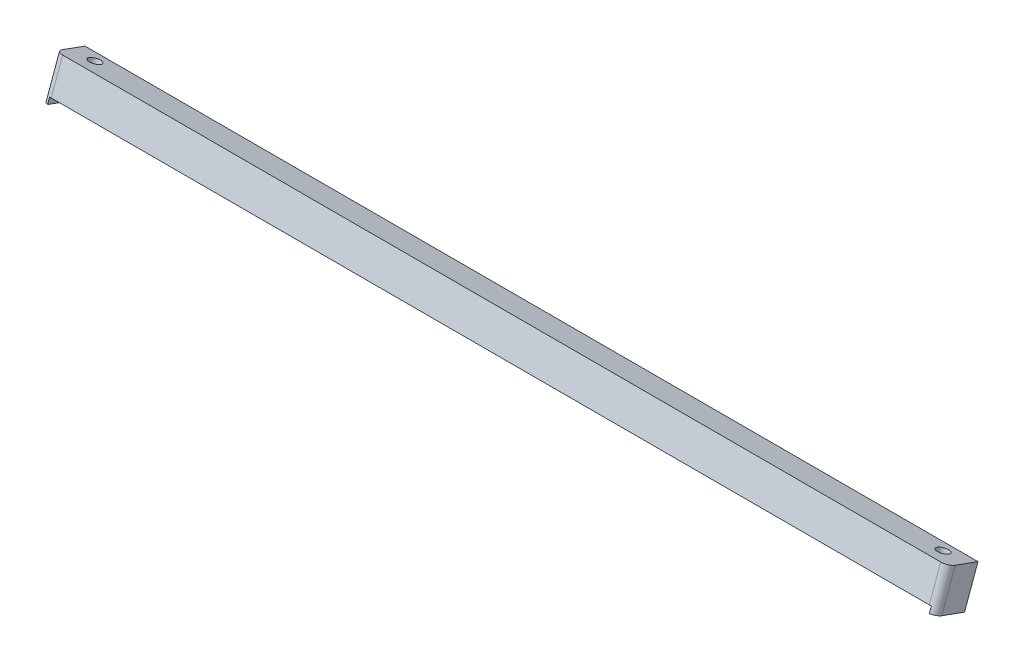
SolidWorks part; units mm, degrees
material "ABS"
ref_plane "Front Plane" through (0, 0, 0) normal (0, 0, 1) x (1, 0, 0)
ref_plane "Top Plane" through (0, 0, 0) normal (0, 1, 0) x (1, 0, 0)
ref_plane "Right Plane" through (0, 0, 0) normal (1, 0, 0) x (0, 0, -1)
sketch "Sketch1" plane through (0, 0, 0) normal (1, 0, 0) x (0, 0, -1)
  line L0 (2.5431, 8.3785) -> (-0.1316, 1.0298)
  line L1 (-0.1316, 1.0298) -> (-8.119, 3.937)
  line L3 (3.1176, 9.9569) -> (-4.8698, 12.8641)
  line L5 (-8.119, 3.937) -> (-4.8698, 12.8641)
  line L6 (2.5431, 8.3785) -> (3.1176, 9.9569)
  dimension "D1" = 8.5
  dimension "D2" = 9.5
extrude "Boss-Extrude1" add sketch "Sketch1" along normal blind 239
sketch "Sketch2" plane through (0, 9.7942, -3.5648) normal (0, 0.9397, -0.342) x (1, 0, 0)
  line L0 (119.5, 1.8524) -> (119.5, -8.9759) construction
  line L1 (240, -10.3299) -> (230.3386, -10.3299) construction
  line L2 (240, -10.3299) -> (240, -0.5476) construction
  line L3 (240, -0.5476) -> (230.3386, -0.5476) construction
  line L4 (230.3386, -10.3299) -> (230.3386, -0.5476) construction
  line L6 (239, -8.9759) -> (0, -8.9759) construction
  line L7 (8.6614, -10.3299) -> (8.6614, -0.5476) construction
  line L8 (-1, -0.5476) -> (8.6614, -0.5476) construction
  line L9 (-1, -10.3299) -> (-1, -0.5476) construction
  line L10 (-1, -10.3299) -> (8.6614, -10.3299) construction
  line L11 (6, -4.0476) -> (233, -4.0476) construction
  line L12 (239, -0.4759) -> (0, -0.4759) construction
  circle A0 centre (233, -4.0476) radius 1.6
  circle A1 centre (6, -4.0476) radius 1.6
  point P18 (119.5, -0.4759)
  dimension "D1" = 113.5
extrude "Cut-Extrude1" cut sketch "Sketch2" against normal through all contours A1 | A0
sketch "Sketch3" plane through (0, 0.8671, -0.3156) normal (0, 0.9397, -0.342) x (1, 0, 0)
  line L0 (239, -8.9759) -> (0, -8.9759) construction
  line L1 (0, -0.4759) -> (1.5, -0.4759)
  line L2 (0, -0.4759) -> (0, -8.9759)
  line L3 (0, -8.9759) -> (1.5, -8.9759)
  line L4 (1.5, -0.4759) -> (1.5, -8.9759)
  line L6 (239, -0.4759) -> (237.5, -0.4759)
  line L7 (239, -0.4759) -> (239, -8.9759)
  line L8 (239, -8.9759) -> (237.5, -8.9759)
  line L9 (237.5, -0.4759) -> (237.5, -8.9759)
  dimension "D1" = 1.5
  dimension "D2" = 1.5
extrude "Boss-Extrude2" add sketch "Sketch3" against normal blind 1.6
fillet "Fillet1" radius 2 2 edges at (239, 7.6488, 6.768) (0, 7.6488, 6.768)
sketch "Sketch4" plane through (0, 9.7942, -3.5648) normal (0, 0.9397, -0.342) x (1, 0, 0)
  line L1 (-30.9525, 25.1195) -> (271.8269, 25.1195)
  line L2 (-30.9525, 25.1195) -> (-30.9525, -23.6135)
  line L3 (-30.9525, -23.6135) -> (271.8269, -23.6135)
  line L4 (271.8269, 25.1195) -> (271.8269, -23.6135)
extrude "Cut-Extrude2" cut sketch "Sketch4" against normal blind 0.55
